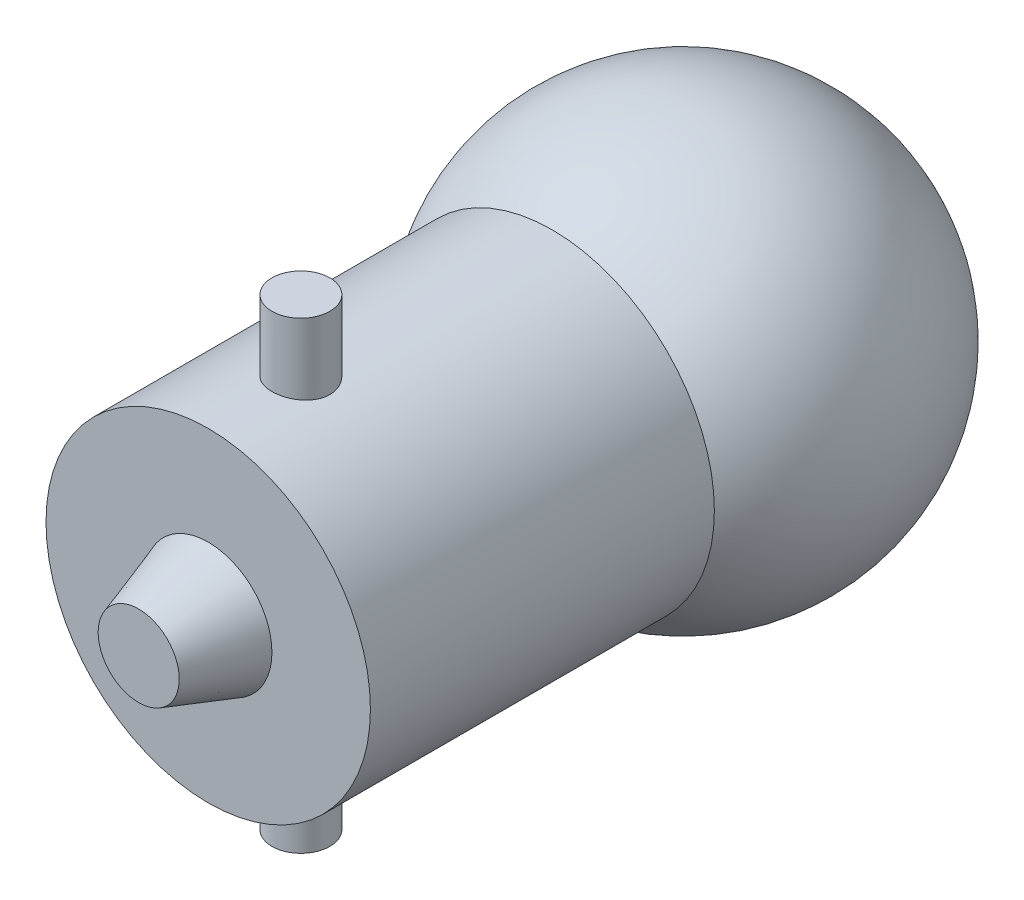
SolidWorks part; units mm, degrees
ref_plane "Face" through (0, 0, 0) normal (0, 0, 1) x (1, 0, 0)
ref_plane "Dessus" through (0, 0, 0) normal (0, 1, 0) x (1, 0, 0)
ref_plane "Droite" through (0, 0, 0) normal (1, 0, 0) x (0, 0, -1)
sketch "Esquisse1" plane through (0, 0, 0) normal (0, 0, 1) x (1, 0, 0)
  circle A0 centre (0, 0) radius 7
  dimension "D1" = 14
extrude "Corps" add sketch "Esquisse1" along normal blind 15
sketch "Esquisse3" plane through (0, 0, 0) normal (1, 0, 0) x (0, 0, -1)
  line L0 (-15, 0) -> (0, 0) construction
  line L1 (5.5, -9) -> (5.5, 9)
  line L3 (5.5, 11.0005) -> (5.5, -13.1684) construction
  line L4 (-15, 7) -> (-15, -7) construction
  arc A0 (5.5, -9) -> (5.5, 9) centre (5.5, 0) ccw
  dimension "D1" = 20.5
  dimension "D2" = 9
revolve "Verre" add sketch "Esquisse3" angle 360 about L3
sketch "Esquisse4" plane through (0, 0, 0) normal (0, 1, 0) x (1, 0, 0)
  line L0 (0, -15) -> (0, -0.1569) construction
  line L1 (-7, -15) -> (7, -15) construction
  circle A0 centre (0, -11) radius 1.25
  dimension "D1" = 2.5
  dimension "D2" = 4
extrude "Baillonettes" add sketch "Esquisse4" along normal mid plane 20
sketch "Esquisse5" plane through (0, 0, 0) normal (1, 0, 0) x (0, 0, -1)
  line L0 (-9.5573, 0) -> (-25.0019, 0) construction
  line L1 (-15, 0) -> (-0.1569, 0) construction
  line L2 (-18, 0) -> (-18, 1.75)
  line L3 (-15, 2.75) -> (-15, 0)
  line L4 (-18, 1.75) -> (-15, 2.75)
  line L5 (-18, 0) -> (-15, 0)
  line L8 (-15, 7) -> (-15, -7) construction
  dimension "D1" = 3
  dimension "D2" = 1.75
  dimension "D3" = 2.75
revolve "Culot" add sketch "Esquisse5" angle 360 about L0
